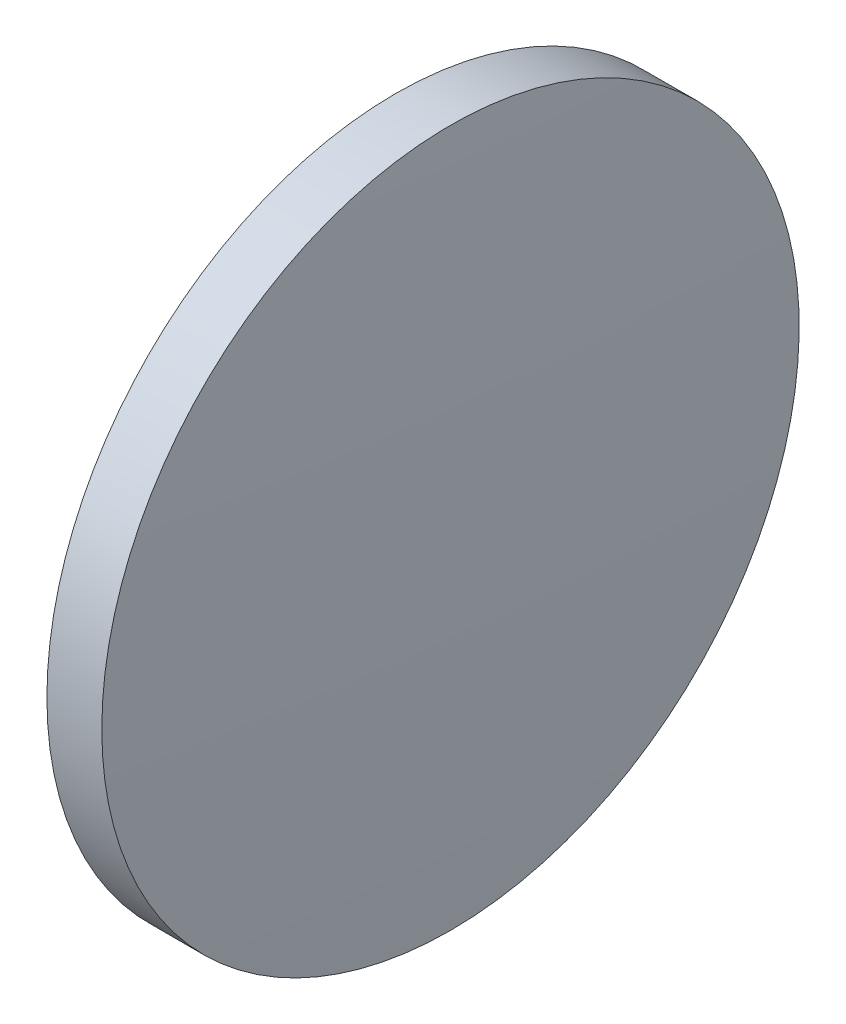
SolidWorks part; units mm, degrees
ref_plane "前视基准面" through (0, 0, 0) normal (0, 0, 1) x (1, 0, 0)
ref_plane "上视基准面" through (0, 0, 0) normal (0, 1, 0) x (1, 0, 0)
ref_plane "右视基准面" through (0, 0, 0) normal (1, 0, 0) x (0, 0, -1)
sketch "草图1" plane through (0, 0, 0) normal (0, 0, 1) x (1, 0, 0)
  line L0 (79.3054, 48.6161) -> (93.4772, 48.6161) construction
  line L1 (85.4585, 61.3161) -> (87.4579, 61.3161)
  line L2 (87.4579, 61.3161) -> (87.4579, 35.9161)
  line L3 (87.4579, 35.9161) -> (85.4585, 35.9161)
  line L4 (85.4585, 35.9161) -> (85.4585, 61.3161)
  arc A0 (85.4585, 61.3161) -> (85.4585, 35.9161) centre (353.856, 48.6161) ccw
  arc A1 (87.4579, 35.9161) -> (87.4579, 61.3161) centre (-180.9396, 48.6161) ccw
  dimension "D1" = 25.4
  dimension "D2" = 1.9993
revolve "旋转1" add sketch "草图1" angle 360 about L0
